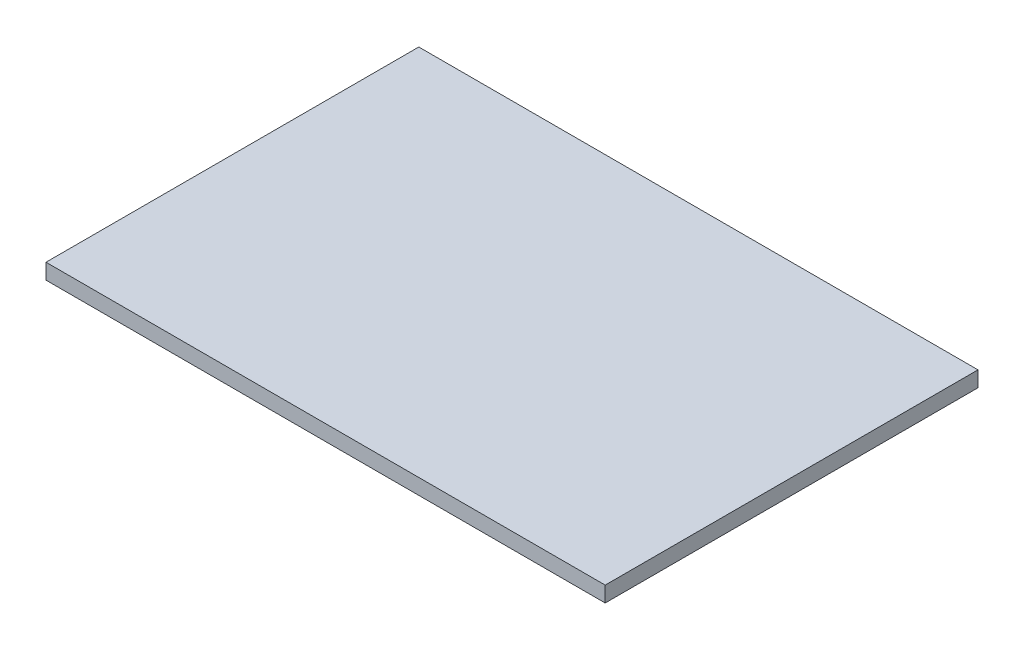
SolidWorks part; units mm, degrees
ref_plane "Front Plane" through (0, 0, 0) normal (0, 0, 1) x (1, 0, 0)
ref_plane "Top Plane" through (0, 0, 0) normal (0, 1, 0) x (1, 0, 0)
ref_plane "Right Plane" through (0, 0, 0) normal (1, 0, 0) x (0, 0, -1)
sketch "Sketch1" plane through (0, 0, 0) normal (0, 1, 0) x (1, 0, 0)
  line L1 (0, 0) -> (57.15, 0)
  line L2 (0, 0) -> (0, 38.1)
  line L3 (0, 38.1) -> (57.15, 38.1)
  line L4 (57.15, 0) -> (57.15, 38.1)
  dimension "D1" = 38.1
  dimension "D2" = 57.15
extrude "Boss-Extrude1" add sketch "Sketch1" along normal blind 1.5875
